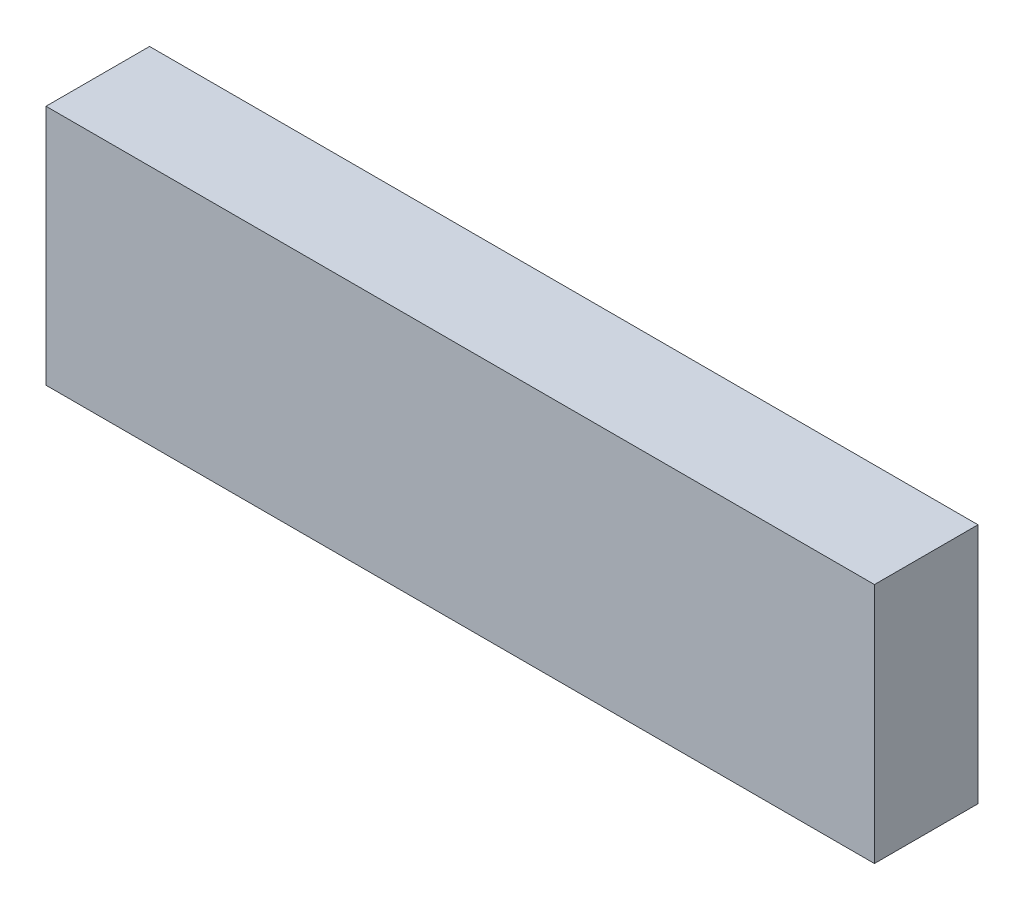
SolidWorks part; units mm, degrees
material "Oak"
ref_plane "Front Plane" through (0, 0, 0) normal (0, 0, 1) x (1, 0, 0)
ref_plane "Top Plane" through (0, 0, 0) normal (0, 1, 0) x (1, 0, 0)
ref_plane "Right Plane" through (0, 0, 0) normal (1, 0, 0) x (0, 0, -1)
sketch "Sketch1" plane through (0, 0, 0) normal (1, 0, 0) x (0, 0, -1)
  line L1 (-19.05, -44.45) -> (19.05, -44.45)
  line L2 (-19.05, -44.45) -> (-19.05, 44.45)
  line L3 (-19.05, 44.45) -> (19.05, 44.45)
  line L4 (19.05, -44.45) -> (19.05, 44.45)
  line L5 (-19.05, -44.45) -> (19.05, 44.45) construction
  line L6 (-19.05, 44.45) -> (19.05, -44.45) construction
  point P0 (0, 0)
  dimension "D1" = 38.1
  dimension "D2" = 88.9
extrude "Boss-Extrude1" add sketch "Sketch1" along normal blind 304.8
